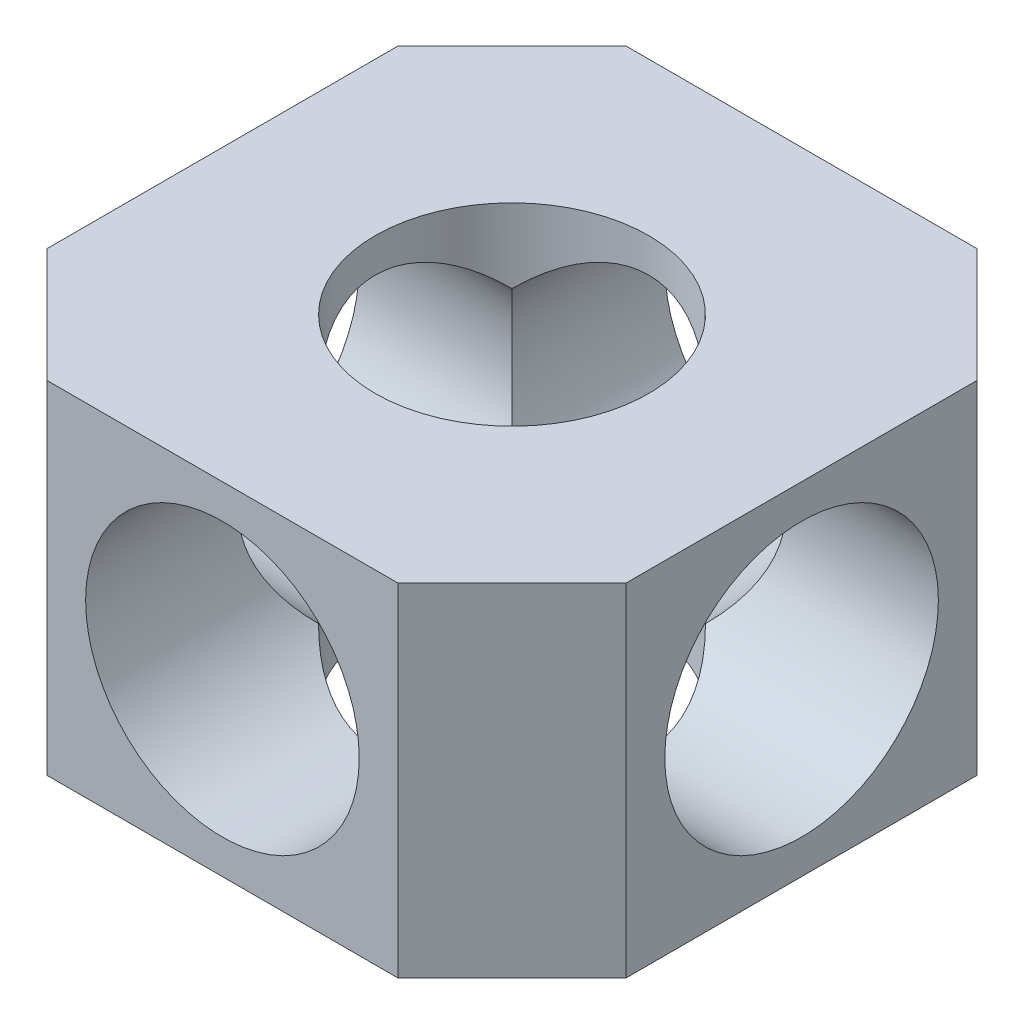
SolidWorks part; units mm, degrees
ref_plane "Ön Düzlem" through (0, 0, 0) normal (0, 0, 1) x (1, 0, 0)
ref_plane "Üst Düzlem" through (0, 0, 0) normal (0, 1, 0) x (1, 0, 0)
ref_plane "Sağ Düzlem" through (0, 0, 0) normal (1, 0, 0) x (0, 0, -1)
sketch "Çizim2" plane through (0, 0, 0) normal (0, 1, 0) x (1, 0, 0)
  line L0 (-12.7, -7.7) -> (-7.7, -12.7)
  line L1 (-7.7, 12.7) -> (7.7, 12.7)
  line L2 (-12.7, 7.7) -> (-12.7, -7.7)
  line L3 (-7.7, -12.7) -> (7.7, -12.7)
  line L4 (12.7, 7.7) -> (12.7, -7.7)
  line L5 (-12.7, 12.7) -> (12.7, -12.7) construction
  line L6 (-12.7, -12.7) -> (12.7, 12.7) construction
  line L7 (7.7, -12.7) -> (12.7, -7.7)
  line L8 (7.7, 12.7) -> (12.7, 7.7)
  line L9 (-12.7, 7.7) -> (-7.7, 12.7)
  circle A0 centre (0, 0) radius 6
  point P0 (0, 0)
  dimension "D3" = 12
  dimension "D1" = 25.4
  dimension "D2" = 25.4
extrude "Yükseklik-Ekstrüzyon1" add sketch "Çizim2" along normal mid plane 15
sketch "Çizim3" plane through (0, 0, 12.7) normal (0, 0, 1) x (1, 0, 0)
  circle A0 centre (0, 0) radius 6
  dimension "D1" = 12
extrude "Kes-Ekstrüzyon1" cut sketch "Çizim3" against normal through all
sketch "Çizim4" plane through (12.7, 0, 0) normal (1, 0, 0) x (0, 0, -1)
  circle A0 centre (0, 0) radius 6
  dimension "D1" = 12
extrude "Kes-Ekstrüzyon2" cut sketch "Çizim4" against normal through all
